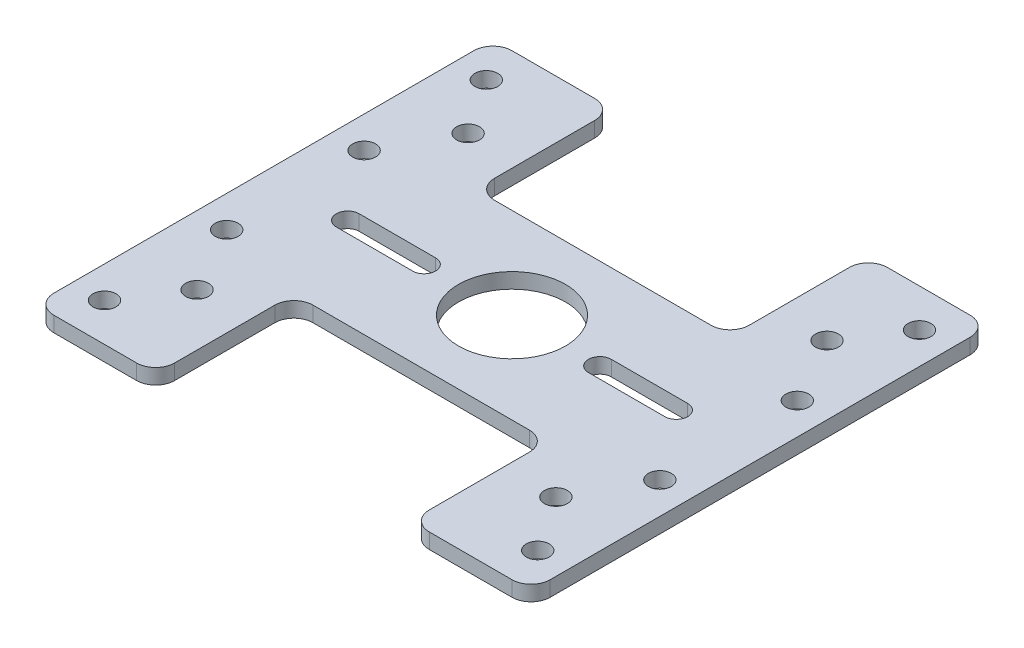
SolidWorks part; units mm, degrees
ref_plane "前视基准面" through (0, 0, 0) normal (0, 0, 1) x (1, 0, 0)
ref_plane "上视基准面" through (0, 0, 0) normal (0, 1, 0) x (1, 0, 0)
ref_plane "右视基准面" through (0, 0, 0) normal (1, 0, 0) x (0, 0, -1)
sketch "草图1" plane through (0, 0, 0) normal (0, 1, 0) x (1, 0, 0)
  line L1 (32.5, 30) -> (-32.5, 30)
  line L2 (32.5, 30) -> (32.5, -30)
  line L3 (32.5, -30) -> (-32.5, -30)
  line L4 (-32.5, 30) -> (-32.5, -30)
  line L5 (32.5, 30) -> (-32.5, -30) construction
  line L6 (32.5, -30) -> (-32.5, 30) construction
  point P0 (0, 0)
extrude "凸台-拉伸1" add sketch "草图1" along normal blind 2
sketch "草图2" plane through (0, 2, 0) normal (0, 1, 0) x (1, 0, 0)
  line L0 (-28.3678, 30) -> (-28.3678, -30) construction
  line L1 (32.5, 30) -> (-32.5, 30) construction
  line L2 (-32.5, -30) -> (32.5, -30) construction
  circle A0 centre (-28.3678, 0) radius 25 construction
  circle A1 centre (-28.3678, 25) radius 1.5
extrude "切除-拉伸1" cut sketch "草图2" against normal blind 2
sketch "草图5" plane through (0, 2, 0) normal (0, 1, 0) x (1, 0, 0)
  circle A0 centre (0, 0) radius 7
extrude "切除-拉伸4" cut sketch "草图5" against normal through all
sketch "草图6" plane through (0, 2, 0) normal (0, 1, 0) x (1, 0, 0)
  line L0 (-32.5, 0) -> (32.5, 0) construction
  line L1 (-32.5, 30) -> (-32.5, -30) construction
  line L2 (32.5, -30) -> (32.5, 30) construction
  line L3 (-28.3678, 25) -> (-28.3678, 0) construction
  line L4 (-28.3678, 0) -> (-28.3678, -9) construction
  circle A0 centre (-28.3678, -9) radius 1.5
  dimension "D1" = 9
extrude "切除-拉伸5" cut sketch "草图6" against normal through all
mirror "镜向7" about plane through (0, 0, 0) normal (0, 0, 1) of "切除-拉伸5"
sketch "草图7" plane through (0, 2, 0) normal (0, 1, 0) x (1, 0, 0)
  line L0 (-32.5, 0) -> (-0.5186, 0) construction
  line L1 (-32.5, 30) -> (-32.5, -30) construction
  line L3 (-11.5093, 1.5) -> (-21.5093, 1.5)
  line L5 (-11.5093, -1.5) -> (-21.5093, -1.5)
  line L7 (-11.5093, 1.5) -> (-21.5093, -1.5) construction
  line L8 (-11.5093, -1.5) -> (-21.5093, 1.5) construction
  arc A0 (-21.5093, 1.5) -> (-21.5093, -1.5) centre (-21.5093, 0) ccw
  arc A1 (-11.5093, 1.5) -> (-11.5093, -1.5) centre (-11.5093, 0) cw
  point P5 (-16.5093, 0)
extrude "切除-拉伸6" cut sketch "草图7" against normal through all
sketch "草图8" plane through (0, 2, 0) normal (0, 1, 0) x (1, 0, 0)
  line L0 (0, 30) -> (0, -30) construction
  line L1 (32.5, 30) -> (-32.5, 30) construction
  line L2 (-32.5, -30) -> (32.5, -30) construction
  line L4 (0, 17.75) -> (23.5, 17.75) construction
  circle A0 centre (23.5, 17.75) radius 1.5
  dimension "D2" = 17.75
  dimension "D1" = 23.5
extrude "切除-拉伸7" cut sketch "草图8" against normal through all
mirror "镜向8" about plane through (0, 0, 0) normal (1, 0, 0) of "镜向7", "切除-拉伸6", "切除-拉伸5"
mirror "镜向9" about plane through (0, 0, 0) normal (0, 0, 1) of "切除-拉伸7", "切除-拉伸1"
mirror "镜向10" about plane through (0, 0, 0) normal (1, 0, 0) of "镜向9", "切除-拉伸1", "切除-拉伸7"
sketch "草图9" plane through (0, 2, 0) normal (0, 1, 0) x (1, 0, 0)
  line L0 (32.5, 30) -> (-32.5, 30) construction
  line L1 (16.6722, 48.1104) -> (-16.6722, 48.1104)
  line L2 (16.6722, 48.1104) -> (16.6722, 11.8896)
  line L3 (16.6722, 11.8896) -> (-16.6722, 11.8896)
  line L4 (-16.6722, 48.1104) -> (-16.6722, 11.8896)
  line L5 (16.6722, 48.1104) -> (-16.6722, 11.8896) construction
  line L6 (16.6722, 11.8896) -> (-16.6722, 48.1104) construction
  point P0 (0, 30)
extrude "切除-拉伸8" cut sketch "草图9" against normal through all
mirror "镜向11" about plane through (0, 0, 0) normal (0, 0, 1) of "切除-拉伸8"
fillet "圆角1" radius 2.5 12 edges at (32.5, 1, 30) (16.6722, 1, 30) (16.6722, 1, 11.8896) (-32.5, 1, 30) (-16.6722, 1, 11.8896) (-16.6722, 1, 30) (32.5, 1, -30) (16.6722, 1, -30) (16.6722, 1, -11.8896) (-16.6722, 1, -11.8896) (-32.5, 1, -30) (-16.6722, 1, -30)
